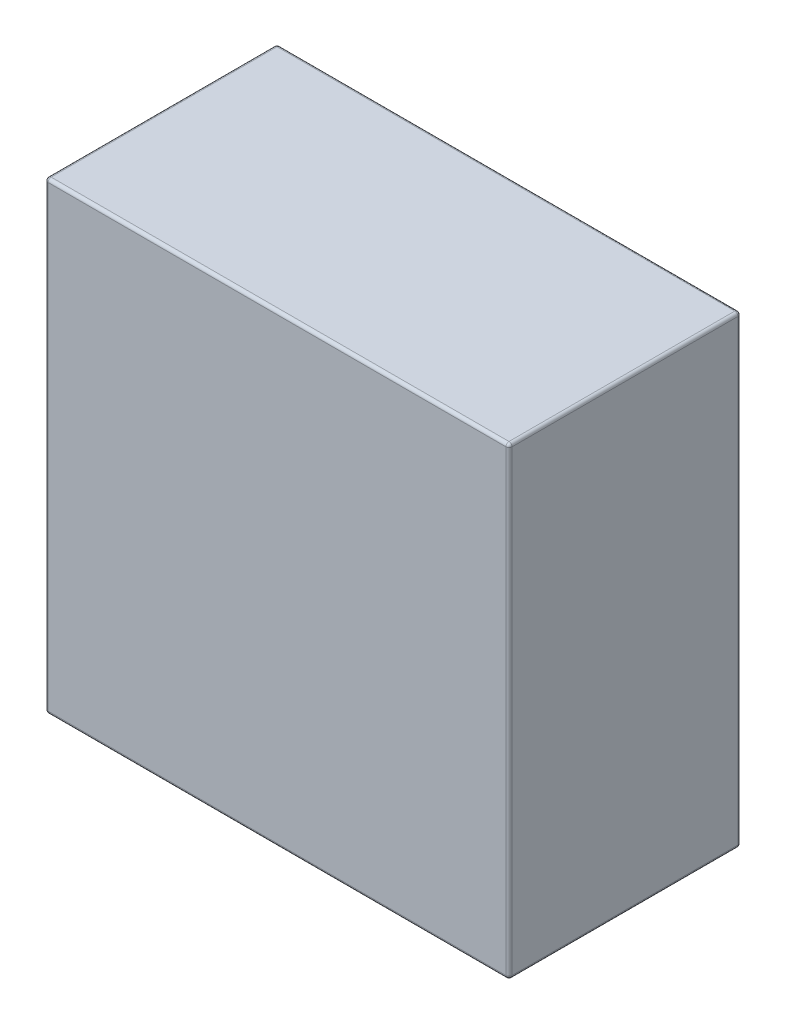
SolidWorks part; units mm, degrees
material "普通碳钢"
ref_plane "Front" through (0, 0, 0) normal (0, 0, 1) x (1, 0, 0)
ref_plane "Top" through (0, 0, 0) normal (0, 1, 0) x (1, 0, 0)
ref_plane "Right" through (0, 0, 0) normal (1, 0, 0) x (0, 0, -1)
sketch "草图1" plane through (0, 0, 0) normal (0, 0, 1) x (1, 0, 0)
  line L1 (0, 0) -> (300, 0)
  line L2 (0, 0) -> (0, 300)
  line L3 (0, 300) -> (300, 300)
  line L4 (300, 0) -> (300, 300)
  dimension "D1" = 300
  dimension "D2" = 300
extrude "凸台-拉伸1" add sketch "草图1" along normal blind 150
fillet "圆角1" radius 2 12 edges at (0, 150, 0) (150, 300, 0) (300, 300, 75) (300, 150, 0) (150, 0, 0) (300, 0, 75) (0, 0, 75) (300, 150, 150) (150, 0, 150) (0, 150, 150) (150, 300, 150) (0, 300, 75)
